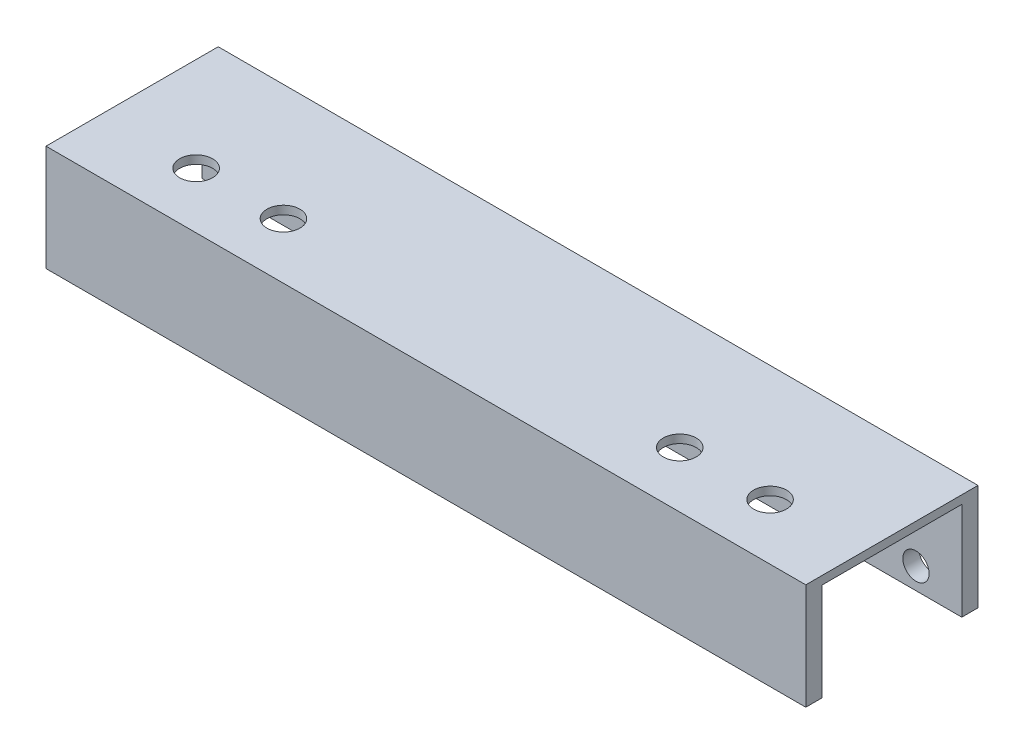
SolidWorks part; units mm, degrees
material "1060 Alloy"
ref_plane "Front Plane" through (0, 0, 0) normal (0, 0, 1) x (1, 0, 0)
ref_plane "Top Plane" through (0, 0, 0) normal (0, 1, 0) x (1, 0, 0)
ref_plane "Right Plane" through (0, 0, 0) normal (1, 0, 0) x (0, 0, -1)
sketch "Sketch1" plane through (0, 0, 0) normal (0, 1, 0) x (1, 0, 0)
  line L1 (0, 0) -> (139.73, 0)
  line L2 (0, 0) -> (0, -31.67)
  line L3 (0, -31.67) -> (139.73, -31.67)
  line L4 (139.73, 0) -> (139.73, -31.67)
  dimension "D1" = 139.73
  dimension "D2" = 31.67
extrude "Boss-Extrude1" add sketch "Sketch1" along normal blind 19.5
sketch "Sketch2" plane through (0, 0, 0) normal (0, -1, 0) x (1, 0, 0)
  line L0 (0, 0) -> (0, 31.67) construction
  line L1 (0, 28.69) -> (139.73, 28.69)
  line L2 (0, 28.69) -> (0, 2.98)
  line L3 (0, 2.98) -> (139.73, 2.98)
  line L4 (139.73, 28.69) -> (139.73, 2.98)
  line L5 (139.73, 31.67) -> (139.73, 0) construction
  dimension "D1" = 2.98
  dimension "D2" = 2.98
extrude "Cut-Extrude1" cut sketch "Sketch2" against normal blind 17.97
hole_wizard "Hole1" positions "Sketch4" profile "Sketch3" legacy end condition up to next
sketch "Sketch4" plane through (0, 0, 0) normal (0, 0, -1) x (-1, 0, 0)
  line L0 (-139.73, 19.5) -> (-139.73, 0) construction
  line L1 (0, 19.5) -> (0, 0) construction
  line L2 (-139.73, 0) -> (0, 0) construction
  point P0 (-131.3, 3.93)
  point P1 (-96.59, 3.93)
  point P3 (-43.14, 3.93)
  point P5 (-8.43, 3.93)
  dimension "D1" = 8.43
  dimension "D2" = 43.14
  dimension "D3" = 8.43
  dimension "D4" = 43.14
  dimension "D5" = 3.93
sketch "Sketch3" plane through (131.3, 3.93, 0) normal (1, 0, 0) x (0, 1, 0)
  line L0 (0, 0) -> (0, 2.98)
  line L1 (0, 2.98) -> (2.42, 2.98)
  line L2 (2.42, 2.98) -> (2.42, 0)
  line L3 (2.42, 0) -> (0, 0)
  line L4 (0, 110) -> (0, -10) construction
  dimension "Diameter" = 4.84
  dimension "Depth" = 2.98
hole_wizard "Hole2" positions "Sketch6" profile "Sketch5" legacy end condition up to next
sketch "Sketch6" plane through (0, 19.5, 0) normal (0, 1, 0) x (-1, 0, 0)
  line L0 (-139.73, 31.67) -> (-139.73, 0) construction
  line L1 (0, 0) -> (0, 31.67) construction
  line L2 (-139.73, 0) -> (0, 0) construction
  point P0 (-122.87, 21.38)
  point P1 (-106.26, 21.38)
  point P3 (-33.38, 21.38)
  point P5 (-17.32, 21.38)
  dimension "D1" = 16.86
  dimension "D2" = 33.47
  dimension "D3" = 33.38
  dimension "D4" = 17.32
  dimension "D5" = 21.38
sketch "Sketch5" plane through (122.87, 19.5, 21.38) normal (1, 0, 0) x (0, 0, 1)
  line L0 (0, 0) -> (0, 1.53)
  line L1 (0, 1.53) -> (3.03, 1.53)
  line L2 (3.03, 1.53) -> (3.03, 0)
  line L3 (3.03, 0) -> (0, 0)
  line L4 (0, 110) -> (0, -10) construction
  dimension "Diameter" = 6.06
  dimension "Depth" = 1.53
equation "\"D2@Sketch2\"=\"D1@Sketch2\""
equation "\"D1@Cut-Extrude1\"=\"D1@Boss-Extrude1\"-0.00153"
